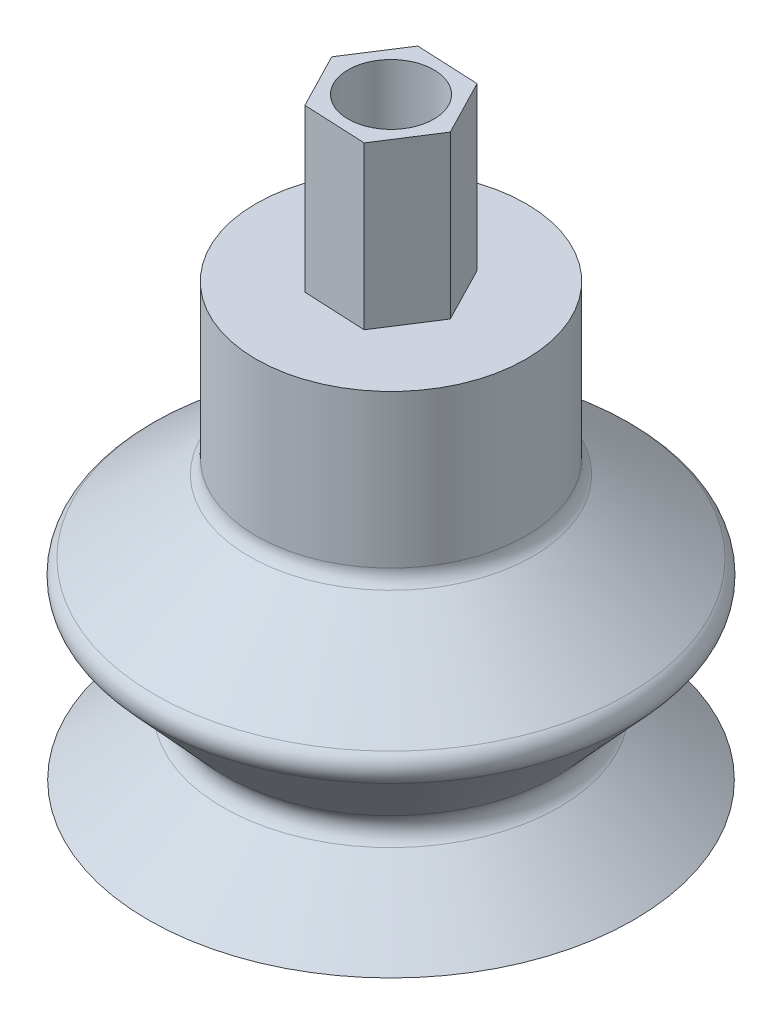
SolidWorks part; units mm, degrees
ref_plane "Front" through (0, 0, 0) normal (0, 0, 1) x (1, 0, 0)
ref_plane "Top" through (0, 0, 0) normal (0, 1, 0) x (1, 0, 0)
ref_plane "Right" through (0, 0, 0) normal (1, 0, 0) x (0, 0, -1)
sketch "Esboço1" plane through (0, 0, 0) normal (0, 0, 1) x (1, 0, 0)
  line L0 (0, 0) -> (13.5, 0)
  line L1 (13.5, 0) -> (8.5, 4)
  line L2 (8.5, 4) -> (14, 10)
  line L3 (14, 10) -> (7.5, 15)
  line L4 (7.5, 15) -> (7.5, 24)
  line L5 (7.5, 24) -> (0, 24)
  line L6 (0, 24) -> (0, 0)
  dimension "D1" = 13.5
  dimension "D2" = 7.5
  dimension "D3" = 14
  dimension "D4" = 8.5
  dimension "D5" = 4
  dimension "D6" = 6
  dimension "D7" = 24
  dimension "D8" = 9
revolve "Revolução1" add sketch "Esboço1" angle 360 about L6
shell "Casca1" thickness 0.9
sketch "Esboço2" plane through (0, 24, 0) normal (0, 1, 0) x (1, 0, 0)
  line L1 (2.4968, 3.8858) -> (-2.1168, 4.1052)
  line L2 (-2.1168, 4.1052) -> (-4.6136, 0.2194)
  line L3 (-4.6136, 0.2194) -> (-2.4968, -3.8858)
  line L4 (-2.4968, -3.8858) -> (2.1168, -4.1052)
  line L5 (2.1168, -4.1052) -> (4.6136, -0.2194)
  line L6 (4.6136, -0.2194) -> (2.4968, 3.8858)
  circle A0 centre (0, 0) radius 4 construction
  dimension "D1" = 8
extrude "Ressalto-extrusão1" add sketch "Esboço2" along normal blind 9
sketch "Esboço3" plane through (0, 33, 0) normal (0, 1, 0) x (1, 0, 0)
  circle A0 centre (0, 0) radius 2.3813
  dimension "D1" = 4.7625
fillet "Filete1" radius 1 3 edges at (-7.5, 15, 0) (-14, 10, 0) (-8.5, 4, 0)
extrude "Corte-extrusão1" cut sketch "Esboço3" against normal through all contours A0
sketch "Esquisse1" plane through (0, 33, 0) normal (0, 1, 0) x (1, 0, 0)
  line L1 (1.5876, -3.0789) -> (3.4602, -0.1645)
  line L2 (3.4602, -0.1645) -> (1.8726, 2.9144)
  line L3 (1.8726, 2.9144) -> (-1.5876, 3.0789)
  line L4 (-1.5876, 3.0789) -> (-3.4602, 0.1645)
  line L5 (-3.4602, 0.1645) -> (-1.8726, -2.9144)
  line L6 (-1.8726, -2.9144) -> (1.5876, -3.0789)
  line L8 (2.4968, 3.8858) -> (-2.1168, 4.1052) construction
  line L9 (2.4968, 3.8858) -> (-2.1168, 4.1052) construction
  circle A0 centre (0, 0) radius 3 construction
  circle A1 centre (0, 0) radius 6.7325
  circle A2 centre (0, 0) radius 2.3813 construction
  dimension "D1" = 1
extrude "Enlèv. mat.-Extru.1" cut sketch "Esquisse1" against normal blind 9
